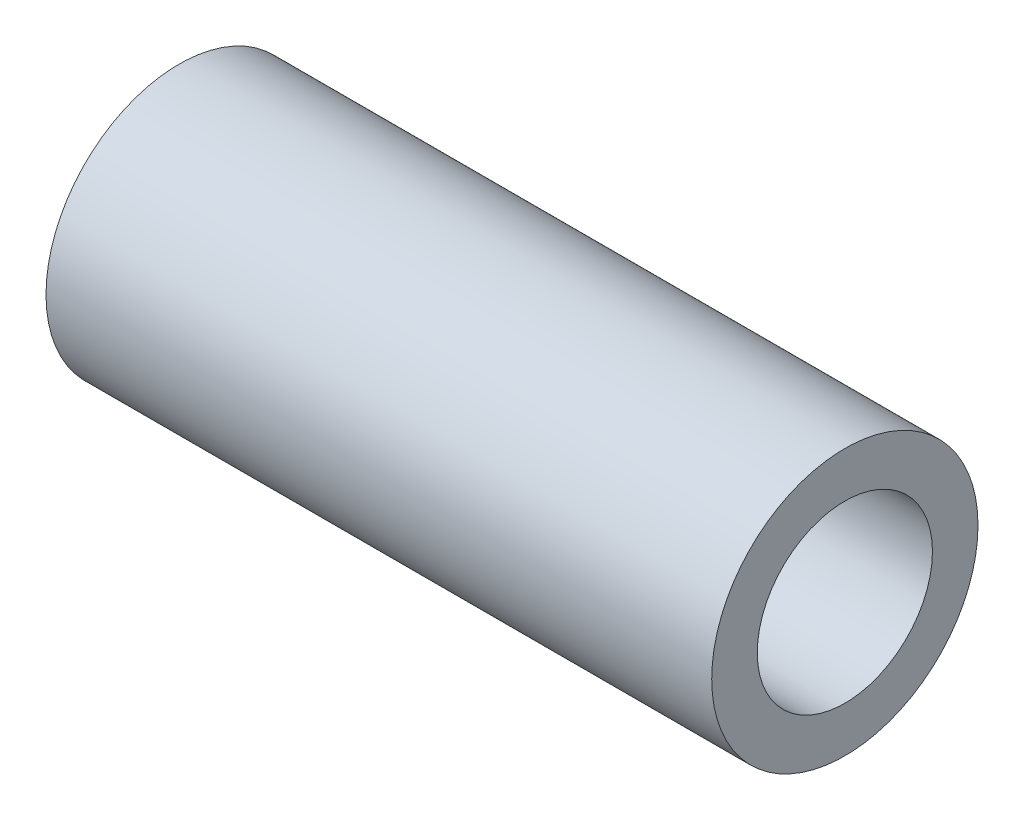
SolidWorks part; units mm, degrees
ref_plane "Front Plane" through (0, 0, 0) normal (0, 0, 1) x (1, 0, 0)
ref_plane "Top Plane" through (0, 0, 0) normal (0, 1, 0) x (1, 0, 0)
ref_plane "Right Plane" through (0, 0, 0) normal (1, 0, 0) x (0, 0, -1)
sketch "Sketch1" plane through (0, 0, 0) normal (1, 0, 0) x (0, 0, -1)
  circle A0 centre (0, 0) radius 24.13
  circle A1 centre (0, 0) radius 15.875
  dimension "D1" = 31.75
  dimension "D2" = 48.26
extrude "Boss-Extrude1" add sketch "Sketch1" along normal blind 120.65
